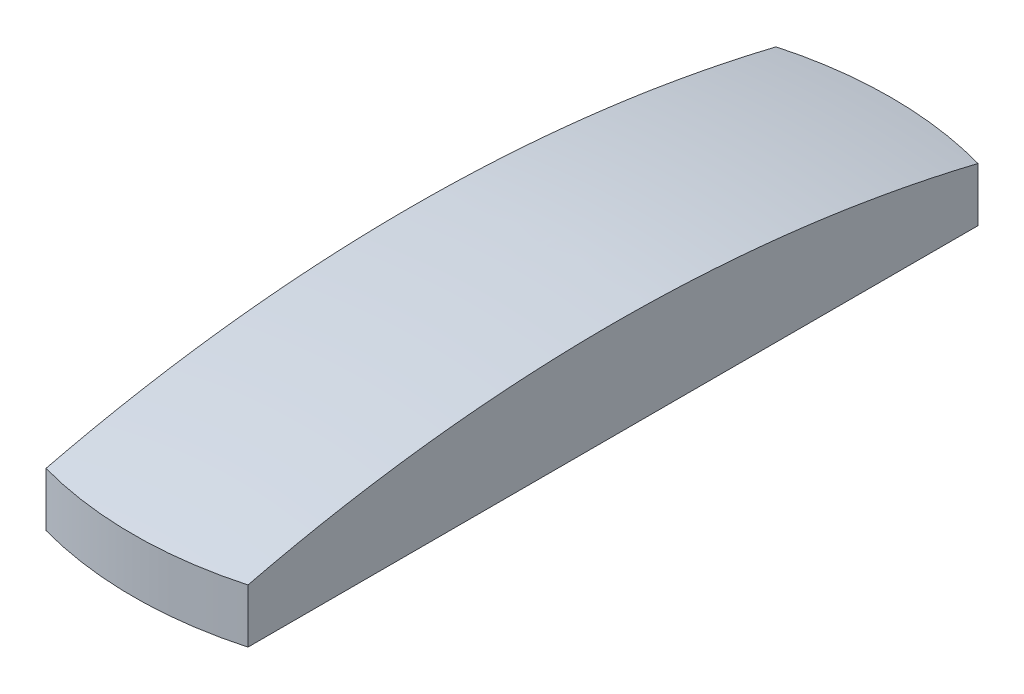
SolidWorks part; units mm, degrees
material "Стекло"
ref_plane "Спереди" through (0, 0, 0) normal (0, 0, 1) x (1, 0, 0)
ref_plane "Сверху" through (0, 0, 0) normal (0, 1, 0) x (1, 0, 0)
ref_plane "Справа" through (0, 0, 0) normal (1, 0, 0) x (0, 0, -1)
sketch "Эскиз1" plane through (0, 0, 0) normal (1, 0, 0) x (0, 0, -1)
  line L0 (0, 2) -> (10.2947, 2) construction
  line L1 (0, 0) -> (7.5, 0)
  line L2 (7.5, 0) -> (7.5, 1.0666)
  line L3 (0, 2) -> (0, 0)
  arc A0 (7.5, 1.0666) -> (0, 2) centre (0, -28.6) ccw
  dimension "D1" = 30.6
  dimension "D2" = 2
  dimension "D3" = 7.5
revolve "Повернуть1" add sketch "Эскиз1" angle 360 about L3
sketch "Эскиз2" plane through (0, 0, 0) normal (0, -1, 0) x (1, 0, 0)
  line L0 (-2, 7.2284) -> (-2, -7.2284)
  line L1 (2, 7.2284) -> (2, -7.2284)
  circle A0 centre (0, 0) radius 7.5 construction
  circle M1 centre (0, 0) radius 7.5
  dimension "D1" = 4
extrude "Вырез-Вытянуть2" cut sketch "Эскиз2" against normal through all contours L0 M1 | L1 M1
chamfer "Фаска1" [suppressed] distance 0.2 angle 45
